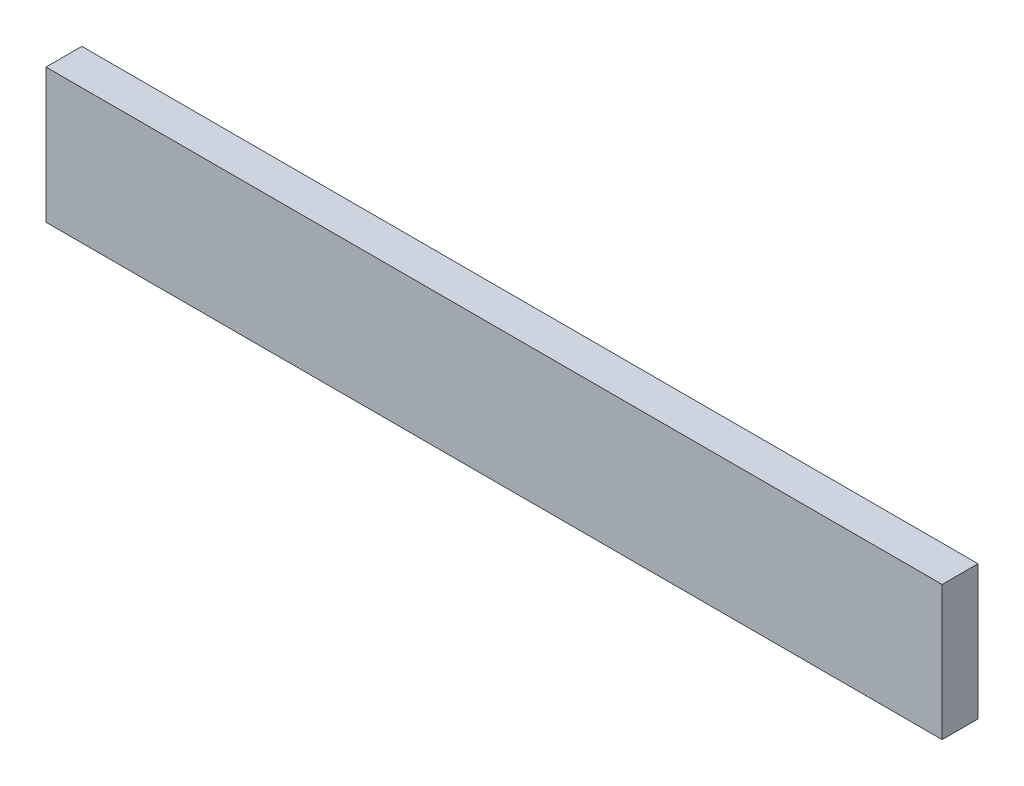
SolidWorks part; units mm, degrees
ref_plane "Front Plane" through (0, 0, 0) normal (0, 0, 1) x (1, 0, 0)
ref_plane "Top Plane" through (0, 0, 0) normal (0, 1, 0) x (1, 0, 0)
ref_plane "Right Plane" through (0, 0, 0) normal (1, 0, 0) x (0, 0, -1)
sketch "Sketch1" plane through (0, 0, 0) normal (0, 0, 1) x (1, 0, 0)
  line L1 (0, 0) -> (127, 0)
  line L2 (0, 0) -> (0, 19.05)
  line L3 (0, 19.05) -> (127, 19.05)
  line L4 (127, 0) -> (127, 19.05)
  dimension "D1" = 19.05
  dimension "D2" = 127
extrude "Boss-Extrude1" add sketch "Sketch1" along normal blind 5.08
sketch "Sketch2" plane through (0, 0, 0) normal (0, 0, -1) x (-1, 0, 0)
  line L0 (0, 0) -> (-127, 0) construction
  circle A0 centre (-109.22, 3.81) radius 2.54
  circle A1 centre (-78.74, 3.81) radius 2.54
  circle A2 centre (-48.26, 3.81) radius 2.54
  circle A3 centre (-17.78, 3.81) radius 2.54
  dimension "D6" = 5.08
  dimension "D7" = 5.08
  dimension "D8" = 5.08
  dimension "D9" = 5.08
  dimension "D1" = 17.78
  dimension "D2" = 30.48
  dimension "D3" = 30.48
  dimension "D4" = 30.48
  dimension "D5" = 3.81
  dimension "D10" = 3.81
  dimension "D11" = 3.81
  dimension "D12" = 3.81
extrude "Boss-Extrude2" add sketch "Sketch2" along normal blind 10.16
